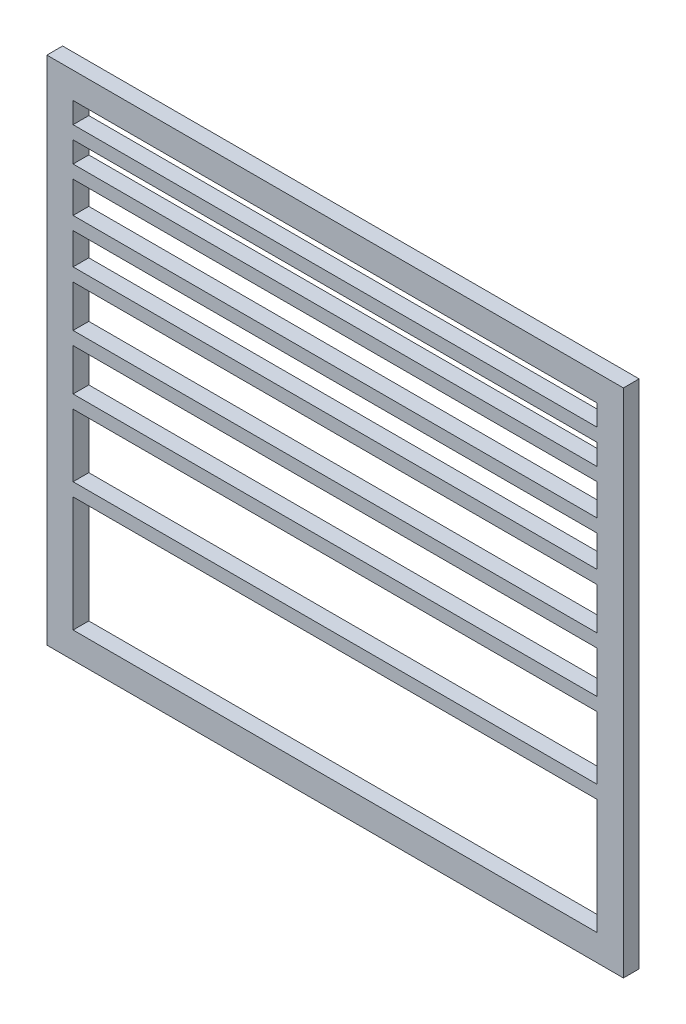
SolidWorks part; units mm, degrees
material "Birch plywood FK"
ref_plane "Спереди" through (0, 0, 0) normal (0, 0, 1) x (1, 0, 0)
ref_plane "Сверху" through (0, 0, 0) normal (0, 1, 0) x (1, 0, 0)
ref_plane "Справа" through (0, 0, 0) normal (1, 0, 0) x (0, 0, -1)
sketch "Эскиз1" plane through (0, 0, 0) normal (0, 0, 1) x (1, 0, 0)
  line L0 (-100, 106) -> (-100, 101) construction
  line L1 (100, 106) -> (-100, 106)
  line L2 (100, 106) -> (100, 114)
  line L3 (100, 114) -> (-100, 114)
  line L4 (-100, 106) -> (-100, 114)
  line L5 (100, 106) -> (-100, 114) construction
  line L6 (100, 114) -> (-100, 106) construction
  line L7 (100, 93) -> (-100, 93)
  line L8 (100, 93) -> (100, 101)
  line L9 (100, 101) -> (-100, 101)
  line L10 (-100, 93) -> (-100, 101)
  line L11 (100, 93) -> (-100, 101) construction
  line L12 (100, 101) -> (-100, 93) construction
  line L13 (100, 76) -> (-100, 76)
  line L14 (100, 76) -> (100, 88)
  line L15 (100, 88) -> (-100, 88)
  line L16 (-100, 76) -> (-100, 88)
  line L17 (100, 76) -> (-100, 88) construction
  line L18 (100, 88) -> (-100, 76) construction
  line L19 (100, 59) -> (-100, 59)
  line L20 (100, 59) -> (100, 71)
  line L21 (100, 71) -> (-100, 71)
  line L22 (-100, 59) -> (-100, 71)
  line L23 (100, 59) -> (-100, 71) construction
  line L24 (100, 71) -> (-100, 59) construction
  line L25 (100, 38) -> (-100, 38)
  line L26 (100, 38) -> (100, 54)
  line L27 (100, 54) -> (-100, 54)
  line L28 (-100, 38) -> (-100, 54)
  line L29 (100, 38) -> (-100, 54) construction
  line L30 (100, 54) -> (-100, 38) construction
  line L31 (100, 17) -> (-100, 17)
  line L32 (100, 17) -> (100, 33)
  line L33 (100, 33) -> (-100, 33)
  line L34 (-100, 17) -> (-100, 33)
  line L35 (100, 17) -> (-100, 33) construction
  line L36 (100, 33) -> (-100, 17) construction
  line L37 (100, -12) -> (-100, -12)
  line L38 (100, -12) -> (100, 12)
  line L39 (100, 12) -> (-100, 12)
  line L40 (-100, -12) -> (-100, 12)
  line L41 (100, -12) -> (-100, 12) construction
  line L42 (100, 12) -> (-100, -12) construction
  line L43 (-100, -12) -> (-100, -17) construction
  line L49 (-100, 93) -> (-100, 88) construction
  line L50 (-100, 76) -> (-100, 71) construction
  line L51 (-100, 59) -> (-100, 54) construction
  line L52 (-100, 38) -> (-100, 33) construction
  line L53 (-100, 17) -> (-100, 12) construction
  line L62 (100, -61) -> (-100, -61)
  line L63 (100, -61) -> (100, -17)
  line L64 (100, -17) -> (-100, -17)
  line L65 (-100, -61) -> (-100, -17)
  line L66 (100, -61) -> (-100, -17) construction
  line L67 (100, -17) -> (-100, -61) construction
  line L70 (110, -71) -> (-110, -71)
  line L71 (110, -71) -> (110, 124)
  line L72 (110, 124) -> (-110, 124)
  line L73 (-110, -71) -> (-110, 124)
  point P0 (0, 110)
  point P5 (0, 97)
  point P10 (0, 82)
  point P15 (0, 65)
  point P20 (0, 46)
  point P25 (0, 25)
  point P30 (0, 0)
  point P45 (0, -39)
  point P50 (0, 12)
  dimension "D1" = 8
  dimension "D2" = 12
  dimension "D3" = 5
  dimension "D4" = 200
  dimension "D5" = 16
  dimension "D6" = 24
  dimension "D7" = 44
  dimension "D8" = 10
  dimension "D9" = 10
  dimension "D10" = 10
  dimension "D11" = 10
extrude "Бобышка-Вытянуть1" add sketch "Эскиз1" along normal blind 6
